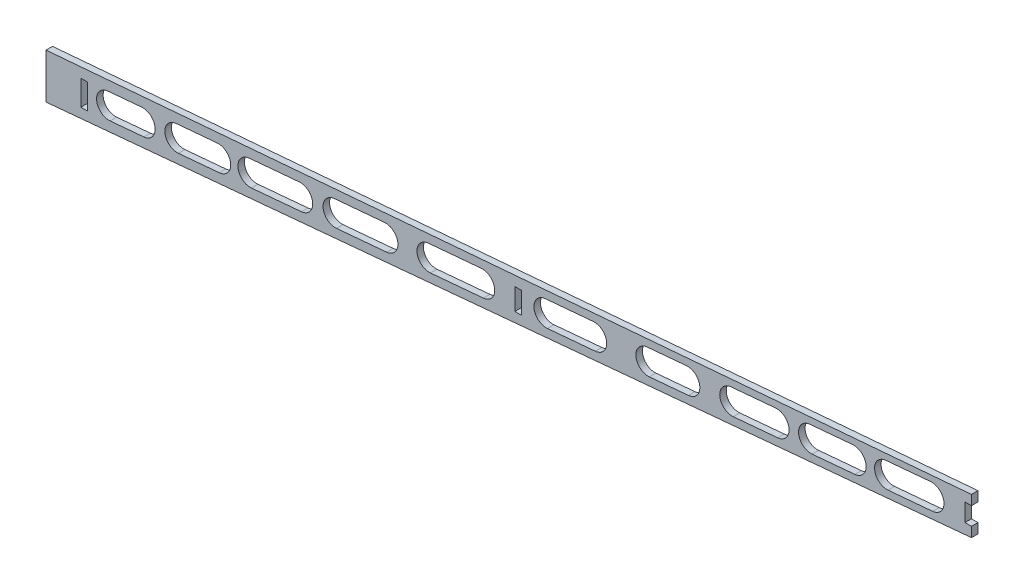
SolidWorks part; units mm, degrees
ref_plane "Front Plane" through (0, 0, 0) normal (0, 0, 1) x (1, 0, 0)
ref_plane "Top Plane" through (0, 0, 0) normal (0, 1, 0) x (1, 0, 0)
ref_plane "Right Plane" through (0, 0, 0) normal (1, 0, 0) x (0, 0, -1)
sketch "Sketch1" plane through (0, 0, 0) normal (0, 0, 1) x (1, 0, 0)
  line L0 (0, 0) -> (0, 20.67)
  line L1 (0, 20.67) -> (425, 56.4764)
  line L2 (425, 56.4764) -> (425, 39.2764)
  line L3 (425, 39.2764) -> (0, 0)
  dimension "D1" = 20.67
  dimension "D2" = 84.72
  dimension "D3" = 425
  dimension "D4" = 17.2
extrude "Boss-Extrude1" add sketch "Sketch1" along normal blind 3
sketch "Sketch2" plane through (0, 0, 3) normal (0, 0, 1) x (1, 0, 0)
  line L0 (425, 39.2764) -> (425, 56.4764) construction
  line L1 (16, 17.518) -> (19, 17.518)
  line L2 (16, 17.518) -> (16, 5.9786)
  line L3 (16, 5.9786) -> (19, 5.9786)
  line L4 (19, 17.518) -> (19, 5.9786)
  line L5 (215.3, 34.3091) -> (218.3, 34.3091)
  line L6 (215.3, 34.3091) -> (215.3, 24.397)
  line L7 (215.3, 24.397) -> (218.3, 24.397)
  line L8 (218.3, 34.3091) -> (218.3, 24.397)
  line L9 (422, 51.9764) -> (425, 51.9764)
  line L10 (422, 51.9764) -> (422, 43.7764)
  line L11 (422, 43.7764) -> (425, 43.7764)
  line L12 (425, 51.9764) -> (425, 43.7764)
  line L13 (215.3, 24.397) -> (215.3, 19.897) construction
  line L14 (0, 0) -> (425, 39.2764) construction
  line L15 (215.3, 34.3091) -> (215.3, 38.8091) construction
  line L16 (425, 56.4764) -> (0, 20.67) construction
  line L17 (16, 22.018) -> (16, 17.518) construction
  line L18 (16, 1.4786) -> (16, 5.9786) construction
  dimension "D1" = 3
  dimension "D2" = 16
  dimension "D3" = 215.3
  dimension "D4" = 4.5
  dimension "D5" = 4.5
  dimension "D6" = 4.5
  dimension "D7" = 4.5
  dimension "D8" = 4.5
  dimension "D9" = 4.5
extrude "Cut-Extrude1" cut sketch "Sketch2" against normal blind 10
sketch "Sketch4" plane through (0, 0, 3) normal (0, 0, 1) x (1, 0, 0)
  line L0 (0, 10.335) -> (422, 47.8764) construction
  line L1 (0, 20.67) -> (0, 0) construction
  line L2 (422, 51.9764) -> (422, 43.7764) construction
  line L3 (28.9352, 12.9091) -> (44.4423, 14.2886) construction
  line L4 (28.4301, 18.5867) -> (43.9373, 19.9662)
  line L5 (29.4402, 7.2315) -> (44.9474, 8.611)
  line L6 (60.296, 15.699) -> (79.1035, 17.3721) construction
  line L7 (59.7909, 21.3766) -> (78.5984, 23.0497)
  line L8 (60.801, 10.0214) -> (79.6086, 11.6945)
  line L9 (229.7622, 30.7748) -> (251.7701, 32.7327) construction
  line L12 (229.2571, 36.4524) -> (251.265, 38.4102)
  line L15 (93.8235, 18.6816) -> (116.7968, 20.7253) construction
  line L16 (93.3185, 24.3592) -> (116.2917, 26.4029)
  line L17 (94.3286, 13.004) -> (117.3019, 15.0478)
  line L18 (132.9191, 22.1596) -> (155.9073, 24.2046) construction
  line L19 (132.4141, 27.8372) -> (155.4022, 29.8822)
  line L20 (133.4242, 16.482) -> (156.4124, 18.5271)
  line L21 (176.0425, 25.9959) -> (200.3583, 28.159) construction
  line L22 (175.5374, 31.6734) -> (199.8532, 33.8366)
  line L23 (176.5476, 20.3183) -> (200.8634, 22.4814)
  line L24 (230.2673, 25.0972) -> (252.2752, 27.0551)
  line L25 (276.5919, 34.9408) -> (294.5612, 36.5394) construction
  line L26 (276.0869, 40.6184) -> (294.0561, 42.217)
  line L27 (277.097, 29.2632) -> (295.0662, 30.8618)
  line L28 (315.0975, 38.3663) -> (335.5479, 40.1856) construction
  line L29 (314.5925, 44.0439) -> (335.0428, 45.8632)
  line L30 (315.6026, 32.6887) -> (336.053, 34.508)
  line L31 (351.2992, 41.5868) -> (370.9286, 43.3331) construction
  line L32 (350.7941, 47.2644) -> (370.4236, 49.0107)
  line L33 (351.8042, 35.9093) -> (371.4337, 37.6555)
  line L34 (386.192, 44.6909) -> (406.6801, 46.5136) construction
  line L35 (385.6869, 50.3685) -> (406.175, 52.1911)
  line L36 (386.6971, 39.0133) -> (407.1852, 40.836)
  arc A0 (28.4301, 18.5867) -> (29.4402, 7.2315) centre (28.9352, 12.9091) ccw
  arc A1 (44.9474, 8.611) -> (43.9373, 19.9662) centre (44.4423, 14.2886) ccw
  arc A2 (59.7909, 21.3766) -> (60.801, 10.0214) centre (60.296, 15.699) ccw
  arc A3 (79.6086, 11.6945) -> (78.5984, 23.0497) centre (79.1035, 17.3721) ccw
  arc A8 (93.3185, 24.3592) -> (94.3286, 13.004) centre (93.8235, 18.6816) ccw
  arc A9 (117.3019, 15.0478) -> (116.2917, 26.4029) centre (116.7968, 20.7253) ccw
  arc A10 (132.4141, 27.8372) -> (133.4242, 16.482) centre (132.9191, 22.1596) ccw
  arc A11 (156.4124, 18.5271) -> (155.4022, 29.8822) centre (155.9073, 24.2046) ccw
  arc A12 (175.5374, 31.6734) -> (176.5476, 20.3183) centre (176.0425, 25.9959) ccw
  arc A13 (200.8634, 22.4814) -> (199.8532, 33.8366) centre (200.3583, 28.159) ccw
  arc A14 (229.2571, 36.4524) -> (230.2673, 25.0972) centre (229.7622, 30.7748) ccw
  arc A15 (252.2752, 27.0551) -> (251.265, 38.4102) centre (251.7701, 32.7327) ccw
  arc A16 (276.0869, 40.6184) -> (277.097, 29.2632) centre (276.5919, 34.9408) ccw
  arc A17 (295.0662, 30.8618) -> (294.0561, 42.217) centre (294.5612, 36.5394) ccw
  arc A18 (314.5925, 44.0439) -> (315.6026, 32.6887) centre (315.0975, 38.3663) ccw
  arc A19 (336.053, 34.508) -> (335.0428, 45.8632) centre (335.5479, 40.1856) ccw
  arc A20 (350.7941, 47.2644) -> (351.8042, 35.9093) centre (351.2992, 41.5868) ccw
  arc A21 (371.4337, 37.6555) -> (370.4236, 49.0107) centre (370.9286, 43.3331) ccw
  arc A22 (385.6869, 50.3685) -> (386.6971, 39.0133) centre (386.192, 44.6909) ccw
  arc A23 (407.1852, 40.836) -> (406.175, 52.1911) centre (406.6801, 46.5136) ccw
  point P8 (36.6887, 13.5989)
  point P13 (69.6997, 16.5355)
  point P22 (240.7661, 31.7537)
  point P27 (285.5765, 35.7401)
  point P34 (105.3102, 19.7035)
  point P39 (144.4132, 23.1821)
  point P48 (188.2004, 27.0774)
  point P55 (325.3227, 39.276)
  point P62 (361.1139, 42.46)
  point P69 (396.4361, 45.6022)
  point P76 (406.7114, 46.162)
  point P77 (386.223, 44.3427)
  point P78 (364.9944, 42.5158)
  point P79 (370.9286, 43.3331)
  dimension "D3" = 5.7
extrude "Cut-Extrude2" cut sketch "Sketch4" against normal blind 76.2
